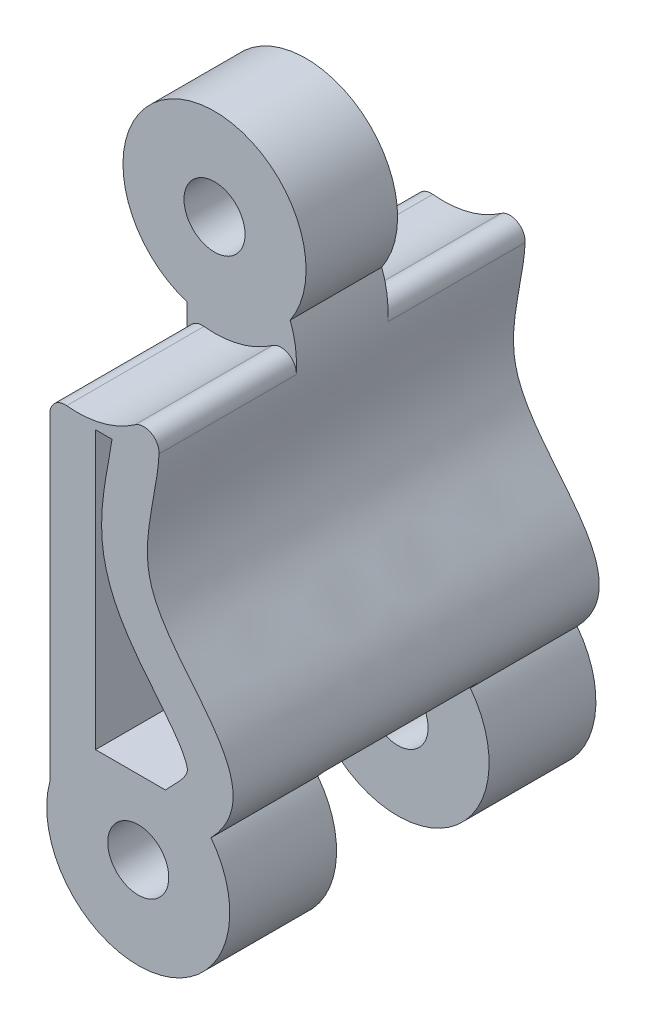
SolidWorks part; units mm, degrees
ref_plane "Front Plane" through (0, 0, 0) normal (0, 0, 1) x (1, 0, 0)
ref_plane "Top Plane" through (0, 0, 0) normal (0, 1, 0) x (1, 0, 0)
ref_plane "Right Plane" through (0, 0, 0) normal (1, 0, 0) x (0, 0, -1)
sketch "Sketch1" plane through (0, 0, 0) normal (0, 0, 1) x (1, 0, 0)
  line L3 (0.7636, 26.9581) -> (0.7636, 41.9581) construction
  line L4 (0.7636, 41.9581) -> (-1.2364, 41.9581) construction
  line L5 (-2.1355, 39.096) -> (-2.1355, 27.7298)
  line L6 (-0.0965, 38.4673) -> (-0.6355, 38.4673)
  line L7 (-0.6355, 38.4673) -> (-0.6355, 29.387)
  line L10 (-0.6355, 40.5838) -> (-0.6355, 27.4991) construction
  line L11 (-0.6355, 29.387) -> (1.6544, 29.387)
  arc A0 (-2.1355, 39.096) -> (1.2411, 40.2664) centre (-1.2364, 41.9581) cw
  arc A2 (-2.1355, 27.7298) -> (3.1486, 28.7779) centre (0.7636, 26.9581) ccw
  circle A3 centre (-1.2364, 41.9581) radius 1
  circle A4 centre (0.7636, 26.9581) radius 1
  arc A7 (-0.6355, 27.4991) -> (0.7636, 28.4581) centre (0.7636, 26.9581) ccw construction
  arc A8 (-0.6355, 40.5838) -> (-0.5234, 40.6384) centre (-1.2364, 41.9581) cw construction
  spline S0 degree 3 poles (1.2411, 40.2664) (1.9123, 38.5893) (-0.8978, 34.0802) (5.3936, 31.1186) (3.1486, 28.7779) knots 0 0 0 0 0.422441 1 1 1 1
  spline S1 degree 1 poles (-0.5234, 40.6384) (0.7636, 28.4581) knots 0 0 1 1 construction
  spline S2 degree 3 poles (-0.5234, 40.6384) (-0.4644, 40.4908) (-0.3758, 40.2694) (-0.2576, 39.9743) (-0.1912, 39.808) (-0.1469, 39.6976) (-0.1382, 39.6745) (-0.1155, 39.6096) (-0.0834, 39.4914) (-0.0387, 39.2136) (-0.0505, 38.793) (-0.1236, 38.2657) (-0.228, 37.6716) (-0.386, 36.83) (-0.4666, 35.8538) (-0.3778, 34.9829) (-0.1242, 34.07) (0.3884, 33.1518) (1.0758, 32.2512) (1.7156, 31.4832) (2.191, 30.839) (2.3837, 30.3917) (2.3756, 30.3058) (2.36, 30.2246) (2.2982, 30.0996) (2.205, 29.9725) (2.1284, 29.8827) (2.0761, 29.8262) (1.9527, 29.6981) (1.8295, 29.5694) (1.7187, 29.454) (1.5021, 29.2282) (1.1965, 28.9095) (0.9081, 28.6088) (0.7636, 28.4581) knots -0.07803 -0.07803 -0.07803 -0.07803 -0.040851 -0.022262 -0.003672 0.000975 0.005623 0.014917 0.033507 0.070686 0.143407 0.180586 0.219402 0.293759 0.368117 0.405296 0.442475 0.516833 0.591191 0.665549 0.739907 0.814265 0.888622 0.925801 0.96298 0.98157 0.990864 1.000159 1.009454 1.018749 1.032978 1.037625 1.074517 1.111696 1.111696 1.111696 1.111696 only from (-0.0965, 38.4673) to (1.6544, 29.387)
  dimension "D1" = 2
  dimension "D2" = 3
  dimension "D3" = 15
  dimension "D4" = 2
  dimension "D5" = 1.5
  dimension "D6" = 6
  dimension "D7" = 1.5
extrude "Boss-Extrude1" add sketch "Sketch1" along normal blind 12
ref_plane "midplane" through (0, 0, 6) normal (0, 0, 1) x (1, 0, 0)
sketch "Sketch2" plane through (0, 0, 12) normal (0, 0, 1) x (1, 0, 0)
  circle A4 centre (-1.2364, 41.9581) radius 3.3
  dimension "D1" = 6.6
extrude "Cut-Extrude1" cut sketch "Sketch2" against normal blind 4.5
mirror "Mirror1" about plane through (0, 0, 6) normal (0, 0, 1) of "Cut-Extrude1"
sketch "Sketch3" plane through (0, 0, 6) normal (0, 0, 1) x (1, 0, 0)
  circle A2 centre (0.7636, 26.9581) radius 3.3
  dimension "D1" = 6.6
extrude "Cut-Extrude2" cut sketch "Sketch3" against normal blind 2.5 and the other way blind 2.5
fillet "Fillet1" radius 0.5 4 edges at (-2.1355, 38.783, 2.25) (-2.1355, 38.783, 9.75) (1.3549, 39.9149, 2.25) (1.3549, 39.9149, 9.75)
equation "\"axle-diameter\"=2"
equation "\"switch-thickness\"=12"
equation "\"base-width\"=6"
equation "\"axle-bushing-radius\"=3"
equation "\"D1@Sketch1\"=\"axle-diameter\""
equation "\"D2@Sketch1\"=\"axle-bushing-radius\""
equation "\"D1@Cut-Extrude1\"=\"switch-thickness\"/3+\"clearance\""
equation "\"D1@Cut-Extrude2\"=\"switch-thickness\"/6+\"clearance\""
equation "\"D2@Cut-Extrude2\"=\"switch-thickness\"/6+\"clearance\""
equation "\"D1@Boss-Extrude1\"=\"switch-thickness\""
equation "\"D1@Sketch2\"=\"axle-bushing-radius\"*2.2"
equation "\"D1@Sketch3\"=\"axle-bushing-radius\"*2.2"
equation "\"clearance\"= 0.5"
